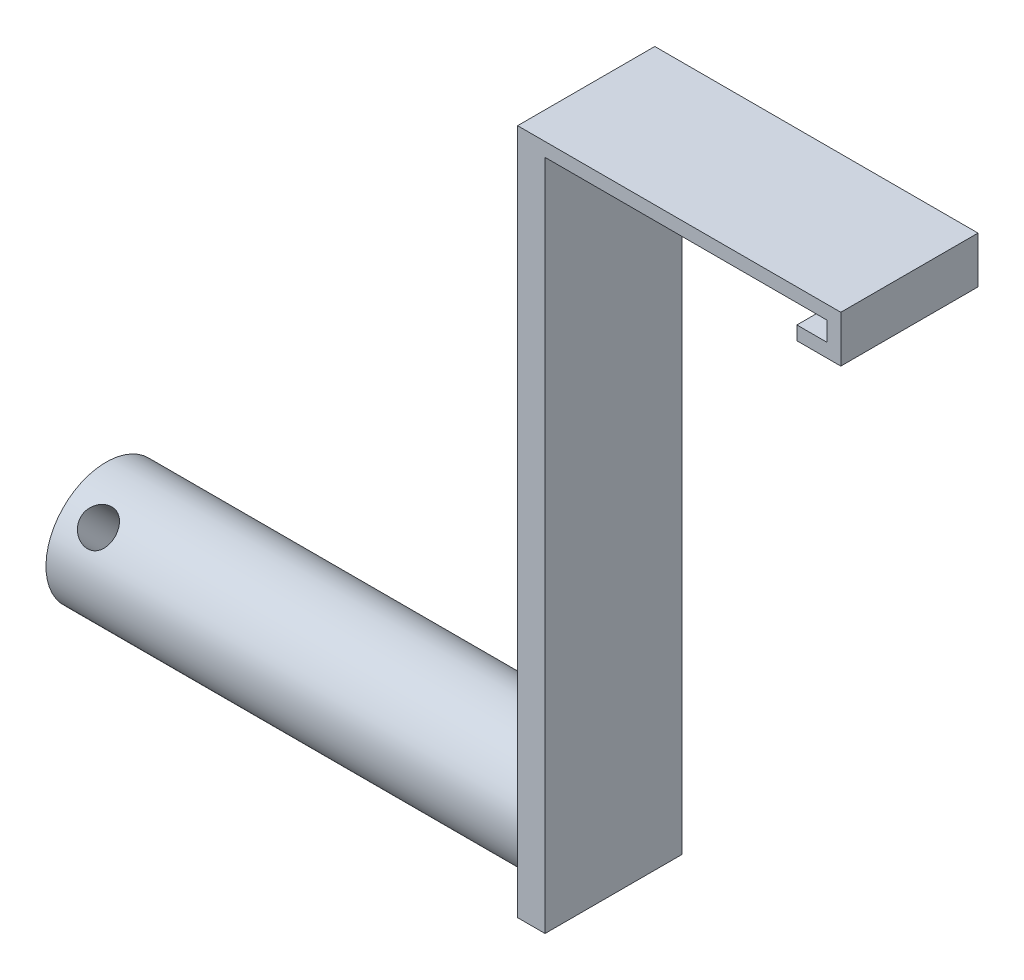
SolidWorks part; units mm, degrees
ref_plane "Front Plane" through (0, 0, 0) normal (0, 0, 1) x (1, 0, 0)
ref_plane "Top Plane" through (0, 0, 0) normal (0, 1, 0) x (1, 0, 0)
ref_plane "Right Plane" through (0, 0, 0) normal (1, 0, 0) x (0, 0, -1)
sketch "Sketch1" plane through (0, 0, 0) normal (0, 0, 1) x (1, 0, 0)
  line L0 (0, 0) -> (5.588, 0)
  line L1 (5.588, 0) -> (5.588, 3.556)
  line L2 (5.588, 3.556) -> (-46.6344, 3.556)
  line L3 (-46.6344, 3.556) -> (-46.6344, -120.904)
  line L4 (-46.6344, -120.904) -> (-51.7144, -120.904)
  line L5 (-51.7144, -120.904) -> (-51.7144, 6.096)
  line L6 (-51.7144, 6.096) -> (8.128, 6.096)
  line L7 (8.128, 6.096) -> (8.128, -2.54)
  line L8 (8.128, -2.54) -> (0, -2.54)
  line L9 (0, -2.54) -> (0, 0)
  dimension "D1" = 59.8424
  dimension "D2" = 2.54
  dimension "D3" = 5.08
  dimension "D4" = 2.54
  dimension "D5" = 2.54
  dimension "D6" = 8.128
  dimension "D7" = 8.636
  dimension "D8" = 127
extrude "Boss-Extrude1" add sketch "Sketch1" along normal blind 25.4
sketch "Sketch2" plane through (-51.7144, 0, 0) normal (-1, 0, 0) x (0, 0, 1)
  line L0 (0, 6.096) -> (0, -120.904) construction
  line L1 (25.4, -120.904) -> (0, -120.904) construction
  circle A0 centre (12.7, -109.7788) radius 11.1252
  dimension "D2" = 22.2504
  dimension "D1" = 12.7
extrude "Boss-Extrude2" add sketch "Sketch2" along normal blind 88.9
ref_plane "Plane1" through (0, -40.6727, -40.6727) normal (0, 0.7071, 0.7071) x (1, 0, 0)
sketch "Sketch3" plane through (0, -40.6727, -40.6727) normal (0, 0.7071, 0.7071) x (1, 0, 0)
  line L0 (-140.6144, -75.4804) -> (-140.6144, -97.7308) construction
  circle A0 centre (-134.2644, -86.6056) radius 3.175
  dimension "D1" = 6.35
  dimension "D2" = 6.35
extrude "Cut-Extrude1" cut sketch "Sketch3" against normal through all
